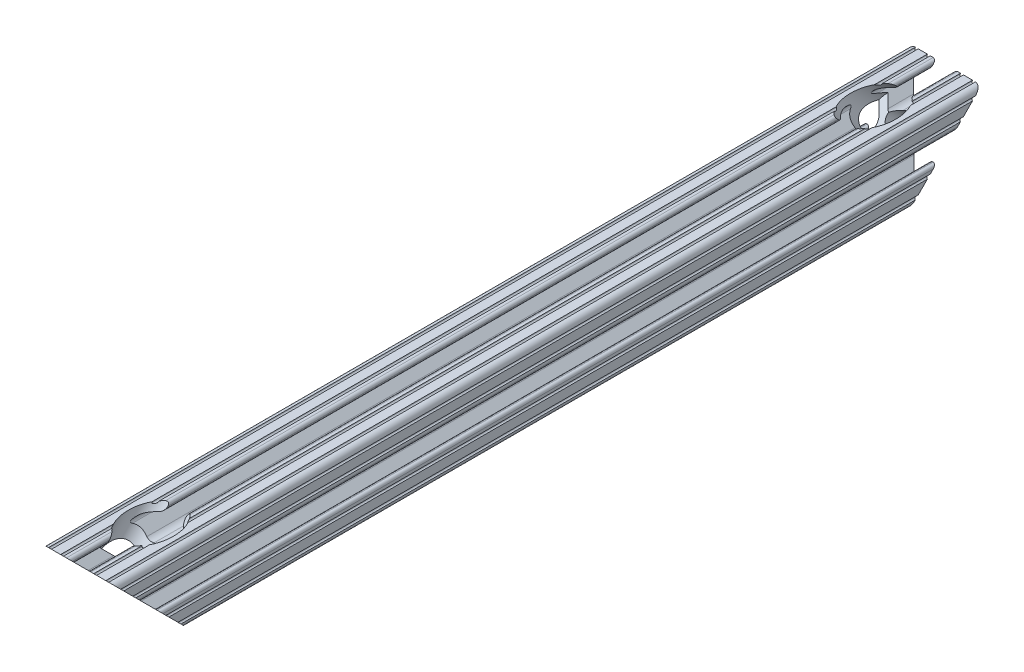
SolidWorks part; units mm, degrees
ref_plane "Front Plane" through (0, 0, 0) normal (0, 0, 1) x (1, 0, 0)
ref_plane "Top Plane" through (0, 0, 0) normal (0, 1, 0) x (1, 0, 0)
ref_plane "Right Plane" through (0, 0, 0) normal (1, 0, 0) x (0, 0, -1)
sketch "Sketch1" plane through (0, 0, 0) normal (0, 0, 1) x (1, 0, 0)
  line L2 (-7.1797, -8.6452) -> (-3.9523, -5.4237)
  line L3 (-1.7093, -4.4958) -> (1.7093, -4.4958)
  line L4 (3.9523, -5.4237) -> (7.1797, -8.6452)
  line L6 (6.4164, -10.4902) -> (4.2875, -10.4902)
  line L7 (3.2385, -11.5392) -> (3.2385, -11.651)
  line L8 (4.2875, -12.7) -> (5.3171, -12.7)
  line L9 (6.3331, -12.7) -> (9.5504, -12.7)
  line L10 (12.7, -9.5504) -> (12.7, -6.3331)
  line L11 (12.7, -5.3171) -> (12.7, -4.2875)
  line L12 (11.651, -3.2385) -> (11.5392, -3.2385)
  line L13 (10.4902, -4.2875) -> (10.4902, -6.4021)
  line L14 (8.7371, -7.1294) -> (5.441, -3.8408)
  line L15 (4.5085, -1.5932) -> (4.5085, 1.5932)
  line L16 (5.441, 3.8408) -> (8.7371, 7.1294)
  line L17 (10.4902, 6.4021) -> (10.4902, 4.2875)
  line L18 (11.5392, 3.2385) -> (11.651, 3.2385)
  line L19 (12.7, 4.2875) -> (12.7, 5.3171)
  line L20 (12.7, 6.3331) -> (12.7, 9.5504)
  line L21 (9.5504, 12.7) -> (6.3331, 12.7)
  line L22 (5.3171, 12.7) -> (4.2875, 12.7)
  line L23 (3.2385, 11.651) -> (3.2385, 11.5392)
  line L24 (4.2875, 10.4902) -> (6.4768, 10.4902)
  line L25 (7.207, 8.7244) -> (3.8983, 5.4232)
  line L26 (1.6558, 4.4958) -> (-1.6558, 4.4958)
  line L27 (-3.8983, 5.4232) -> (-7.207, 8.7244)
  line L28 (-6.4768, 10.4902) -> (-4.2875, 10.4902)
  line L29 (-3.2385, 11.5392) -> (-3.2385, 11.651)
  line L30 (-4.2875, 12.7) -> (-5.3171, 12.7)
  line L31 (-6.3331, 12.7) -> (-9.5504, 12.7)
  line L32 (-12.7, 9.5504) -> (-12.7, 6.3331)
  line L33 (-12.7, 5.3171) -> (-12.7, 4.2875)
  line L34 (-11.651, 3.2385) -> (-11.5392, 3.2385)
  line L35 (-10.4902, 4.2875) -> (-10.4902, 6.4021)
  line L36 (-8.7371, 7.1294) -> (-5.441, 3.8408)
  line L37 (-4.5085, 1.5932) -> (-4.5085, -1.5932)
  line L38 (-5.441, -3.8408) -> (-8.7371, -7.1294)
  line L39 (-10.4902, -6.4021) -> (-10.4902, -4.2875)
  line L40 (-11.5392, -3.2385) -> (-11.651, -3.2385)
  line L41 (-12.7, -4.2875) -> (-12.7, -5.3171)
  line L42 (-12.7, -6.3331) -> (-12.7, -9.5504)
  line L43 (-9.5504, -12.7) -> (-6.3331, -12.7)
  line L44 (-5.3171, -12.7) -> (-4.2875, -12.7)
  line L45 (-3.2385, -11.651) -> (-3.2385, -11.5392)
  line L46 (-4.2875, -10.4902) -> (-6.4164, -10.4902)
  circle A0 centre (0, 0) radius 2.6035
  arc A1 (-7.1797, -8.6452) -> (-6.4164, -10.4902) centre (-6.4164, -9.4098) ccw
  arc A2 (-1.7093, -4.4958) -> (-3.9523, -5.4237) centre (-1.7093, -7.6708) ccw
  arc A3 (3.9523, -5.4237) -> (1.7093, -4.4958) centre (1.7093, -7.6708) ccw
  arc A4 (6.4164, -10.4902) -> (7.1797, -8.6452) centre (6.4164, -9.4098) ccw
  arc A5 (4.2875, -10.4902) -> (3.2385, -11.5392) centre (4.2875, -11.5392) ccw
  arc A6 (3.2385, -11.651) -> (4.2875, -12.7) centre (4.2875, -11.651) ccw
  arc A7 (6.3331, -12.7) -> (5.3171, -12.7) centre (5.8251, -12.7) ccw
  arc A8 (10.5664, -12.6998) -> (9.5504, -12.7) centre (10.0584, -12.7) ccw
  arc A9 (10.5664, -12.6998) -> (12.6998, -10.5664) centre (10.5918, -10.5918) ccw
  arc A10 (12.7, -9.5504) -> (12.6998, -10.5664) centre (12.7, -10.0584) ccw
  arc A11 (12.7, -5.3171) -> (12.7, -6.3331) centre (12.7, -5.8251) ccw
  arc A12 (12.7, -4.2875) -> (11.651, -3.2385) centre (11.651, -4.2875) ccw
  arc A13 (11.5392, -3.2385) -> (10.4902, -4.2875) centre (11.5392, -4.2875) ccw
  arc A14 (8.7371, -7.1294) -> (10.4902, -6.4021) centre (9.4628, -6.4021) ccw
  arc A15 (4.5085, -1.5932) -> (5.441, -3.8408) centre (7.6835, -1.5932) ccw
  arc A16 (5.441, 3.8408) -> (4.5085, 1.5932) centre (7.6835, 1.5932) ccw
  arc A17 (10.4902, 6.4021) -> (8.7371, 7.1294) centre (9.4628, 6.4021) ccw
  arc A18 (10.4902, 4.2875) -> (11.5392, 3.2385) centre (11.5392, 4.2875) ccw
  arc A19 (11.651, 3.2385) -> (12.7, 4.2875) centre (11.651, 4.2875) ccw
  arc A20 (12.7, 6.3331) -> (12.7, 5.3171) centre (12.7, 5.8251) ccw
  arc A21 (12.6998, 10.5664) -> (12.7, 9.5504) centre (12.7, 10.0584) ccw
  arc A22 (12.6998, 10.5664) -> (10.5664, 12.6998) centre (10.5918, 10.5918) ccw
  arc A23 (9.5504, 12.7) -> (10.5664, 12.6998) centre (10.0584, 12.7) ccw
  arc A24 (5.3171, 12.7) -> (6.3331, 12.7) centre (5.8251, 12.7) ccw
  arc A25 (4.2875, 12.7) -> (3.2385, 11.651) centre (4.2875, 11.651) ccw
  arc A26 (3.2385, 11.5392) -> (4.2875, 10.4902) centre (4.2875, 11.5392) ccw
  arc A27 (7.207, 8.7244) -> (6.4768, 10.4902) centre (6.4768, 9.4563) ccw
  arc A28 (1.6558, 4.4958) -> (3.8983, 5.4232) centre (1.6558, 7.6708) ccw
  arc A29 (-3.8983, 5.4232) -> (-1.6558, 4.4958) centre (-1.6558, 7.6708) ccw
  arc A30 (-6.4768, 10.4902) -> (-7.207, 8.7244) centre (-6.4768, 9.4563) ccw
  arc A31 (-4.2875, 10.4902) -> (-3.2385, 11.5392) centre (-4.2875, 11.5392) ccw
  arc A32 (-3.2385, 11.651) -> (-4.2875, 12.7) centre (-4.2875, 11.651) ccw
  arc A33 (-6.3331, 12.7) -> (-5.3171, 12.7) centre (-5.8251, 12.7) ccw
  arc A34 (-10.5664, 12.6998) -> (-9.5504, 12.7) centre (-10.0584, 12.7) ccw
  arc A35 (-10.5664, 12.6998) -> (-12.6998, 10.5664) centre (-10.5918, 10.5918) ccw
  arc A36 (-12.7, 9.5504) -> (-12.6998, 10.5664) centre (-12.7, 10.0584) ccw
  arc A37 (-12.7, 5.3171) -> (-12.7, 6.3331) centre (-12.7, 5.8251) ccw
  arc A38 (-12.7, 4.2875) -> (-11.651, 3.2385) centre (-11.651, 4.2875) ccw
  arc A39 (-11.5392, 3.2385) -> (-10.4902, 4.2875) centre (-11.5392, 4.2875) ccw
  arc A40 (-8.7371, 7.1294) -> (-10.4902, 6.4021) centre (-9.4628, 6.4021) ccw
  arc A41 (-4.5085, 1.5932) -> (-5.441, 3.8408) centre (-7.6835, 1.5932) ccw
  arc A42 (-5.441, -3.8408) -> (-4.5085, -1.5932) centre (-7.6835, -1.5932) ccw
  arc A43 (-10.4902, -6.4021) -> (-8.7371, -7.1294) centre (-9.4628, -6.4021) ccw
  arc A44 (-10.4902, -4.2875) -> (-11.5392, -3.2385) centre (-11.5392, -4.2875) ccw
  arc A45 (-11.651, -3.2385) -> (-12.7, -4.2875) centre (-11.651, -4.2875) ccw
  arc A46 (-12.7, -6.3331) -> (-12.7, -5.3171) centre (-12.7, -5.8251) ccw
  arc A47 (-12.6998, -10.5664) -> (-12.7, -9.5504) centre (-12.7, -10.0584) ccw
  arc A48 (-12.6998, -10.5664) -> (-10.5664, -12.6998) centre (-10.5918, -10.5918) ccw
  arc A49 (-9.5504, -12.7) -> (-10.5664, -12.6998) centre (-10.0584, -12.7) ccw
  arc A50 (-5.3171, -12.7) -> (-6.3331, -12.7) centre (-5.8251, -12.7) ccw
  arc A51 (-4.2875, -12.7) -> (-3.2385, -11.651) centre (-4.2875, -11.651) ccw
  arc A52 (-3.2385, -11.5392) -> (-4.2875, -10.4902) centre (-4.2875, -11.5392) ccw
extrude "Boss-Extrude1" add sketch "Sketch1" along normal mid plane 304.8
sketch "Sketch2" plane through (0, 0, 0) normal (1, 0, 0) x (0, 0, -1)
  line L0 (-152.4, 12.6998) -> (-152.4, -12.7)
  line L1 (-152.4, -12.7) -> (-127.0002, -12.7)
  line L2 (-127.0002, -12.7) -> (-152.4, 12.6998)
  line L3 (0, 0) -> (0, -12.7) construction
  line L5 (127.0002, -12.7) -> (152.4, 12.6998)
  line L6 (152.4, -12.7) -> (127.0002, -12.7)
  line L7 (152.4, 12.6998) -> (152.4, -12.7)
  line L8 (-152.4, -12.7) -> (152.4, -12.7) construction
extrude "Cut-Extrude1" cut sketch "Sketch2" against normal through all and the other way through all
sketch "Sketch3" plane through (0, 0, 0) normal (1, 0, 0) x (0, 0, -1)
  line L0 (-121.3876, 18.3125) -> (-139.7002, 0)
  line L1 (-139.7002, 0) -> (-142.0081, 2.3079)
  line L2 (-142.0081, 2.3079) -> (-137.518, 6.7981)
  line L3 (-137.518, 6.7981) -> (-140.8227, 10.1028)
  line L4 (-140.8227, 10.1028) -> (-127.0003, 23.9252)
  line L5 (-127.0003, 23.9252) -> (-121.3876, 18.3125)
  line L6 (-139.7002, 0) -> (-142.0081, -2.3079) construction
  line L7 (-127.0002, -12.7) -> (-152.4, 12.6998) construction
  line L8 (-142.3037, 2.6035) -> (-137.0967, -2.6035) construction
  line L9 (-129.5974, -1.1225) -> (-115.775, 12.6998) construction
  dimension "D1" = 6.5278
  dimension "D2" = 15.875
  dimension "D3" = 6.35
revolve "Cut-Revolve1" cut sketch "Sketch3" angle 360 mid plane about L6
mirror "Mirror1" about plane through (0, 0, 0) normal (0, 0, 1) of "Cut-Revolve1"
